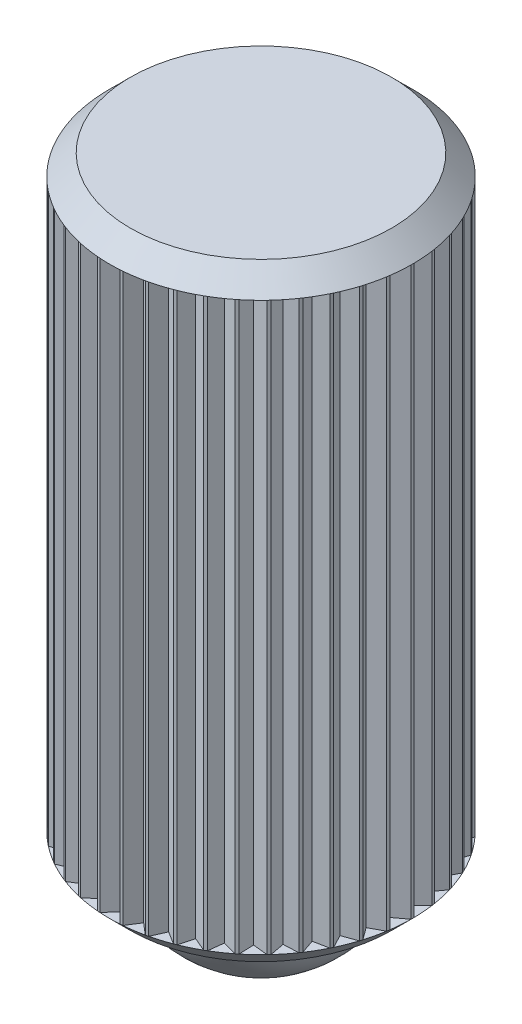
SolidWorks part; units mm, degrees
ref_plane "Front" through (0, 0, 0) normal (0, 0, 1) x (1, 0, 0)
ref_plane "Top" through (0, 0, 0) normal (0, 1, 0) x (1, 0, 0)
ref_plane "Right" through (0, 0, 0) normal (1, 0, 0) x (0, 0, -1)
sketch "Sketch24" plane through (0, 0, 0) normal (1, 0, 0) x (0, 0, -1)
  line L5 (0, 7.493) -> (0, -7.493) construction
  line L6 (-2.3876, -5.8798) -> (-2.3876, -4.1233) construction
  line L7 (-2.8385, -5.715) -> (-2.8384, 7.493) construction
  line L8 (-2.8385, -5.715) -> (-3.2893, -5.2641)
  line L9 (-2.8385, -5.715) -> (-3.2893, -5.715) construction
  line L10 (-3.2893, -5.2641) -> (-3.2893, 7.0421)
  line L11 (-3.2893, 7.0421) -> (-2.8384, 7.493)
  line L12 (-2.8384, 7.493) -> (0, 7.493)
  line L13 (0, -7.493) -> (0, 7.493) construction
  line L16 (-2.8385, -5.715) -> (-2.3876, -5.715)
  line L17 (-3.1369, -4.1233) -> (0, -4.1233) construction
  line L18 (0, -4.1233) -> (0, 7.493)
  line L19 (-2.3876, -5.715) -> (-2.3876, -4.1233)
  line L20 (-2.3876, -4.1233) -> (0, -4.1233)
  circle A1 centre (0, -5.1054) radius 2.3876 construction
  dimension "Ball Dia" = 4.7752
  dimension "Body Dia" = 6.5786
  dimension "D2" = 45
  dimension "Ball Projection" = 1.778
  dimension "D1" = 13.208
  dimension "D3" = 1.5917
  dimension "D4" = 45
revolve "Revolve2" add sketch "Sketch24" angle 360 about L5
ref_plane "Plane1" through (0, -5.2641, 0) normal (0, 1, 0) x (-1, 0, 0)
sketch "Sketch26" plane through (0, -5.2641, 0) normal (0, 1, 0) x (-1, 0, 0)
  line L0 (0, 0) -> (0.2151, 3.2823) construction
  line L1 (0, 0) -> (-0.2151, 3.2823) construction
  line L2 (0, 3.0353) -> (0.2151, 3.2823)
  line L3 (0, 3.0353) -> (-0.2151, 3.2823)
  circle A1 centre (0, 0) radius 3.2893 construction
  circle A2 centre (0, 0) radius 3.0353
  circle A3 centre (0, 0) radius 3.0353 construction
  arc A4 (0.2151, 3.2823) -> (-0.2151, 3.2823) centre (0, 0) ccw
  dimension "D2" = 7.5
  dimension "D1" = 0.254
extrude "Extrude1" cut sketch "Sketch26" along normal up to vertex (12.3063 mm away) up to point (0, 7.0421, 3.2893)
pattern_circular "CirPattern1" count 42 over 360 about axis through (0, 0, 0) along (0, 1, 0) of "Extrude1"
sketch "Sketch25" plane through (0, 0, 0) normal (1, 0, 0) x (0, 0, -1)
  line L0 (0, -7.493) -> (0, -2.7178)
  circle A0 centre (0, -5.1054) radius 2.3876 construction
  arc A2 (0, -7.493) -> (0, -2.7178) centre (0, -5.1054) cw
revolve "Revolve3" add sketch "Sketch25" angle 360 about L18
sketch "Sketch27" plane through (0, 0, 0) normal (0, 1, 0) x (1, 0, 0)
  circle A0 centre (0, 0) radius 3.2893
  arc A1 (1.2303, -3.0506) -> (1.6179, -2.8639) centre (0, 0) ccw construction
equation "\"D3@Sketch24\" = \"Ball Dia@Sketch24\"/3"
